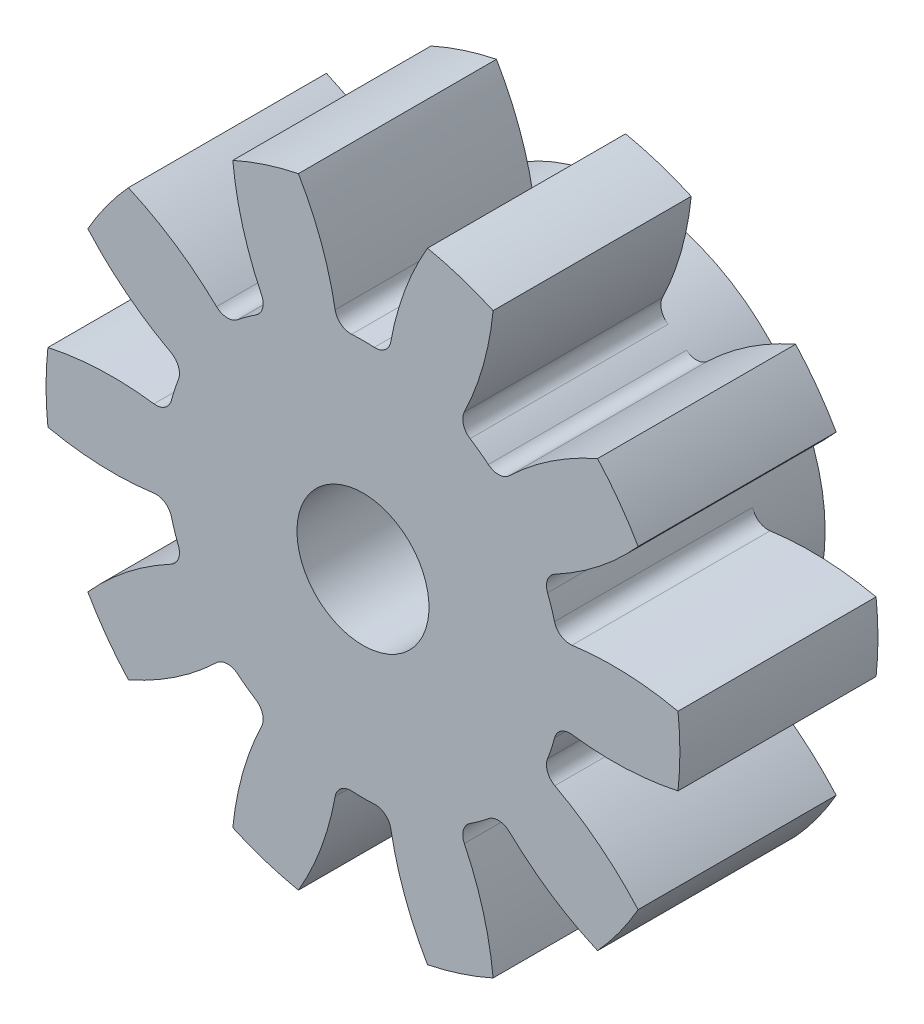
SolidWorks part; units mm, degrees
ref_plane "Front Plane" through (0, 0, 0) normal (0, 0, 1) x (1, 0, 0)
ref_plane "Top Plane" through (0, 0, 0) normal (0, 1, 0) x (1, 0, 0)
ref_plane "Right Plane" through (0, 0, 0) normal (1, 0, 0) x (0, 0, -1)
sketch "Sketch1" plane through (0, 0, 0) normal (0, 0, 1) x (1, 0, 0)
  circle A0 centre (0, 0) radius 10
  circle A1 centre (0, 0) radius 12
  circle A2 centre (0, 0) radius 7.5
  dimension "D1" = 20
  dimension "D2" = 24
  dimension "D3" = 4.5
extrude "Boss-Extrude1" add sketch "Sketch1" along normal mid plane 425 contours A1
sketch "Sketch2" plane through (0, 0, 0) normal (0, 0, 1) x (1, 0, 0)
  line L0 (0, 0) -> (0, 12) construction
  line L1 (-1.5643, 9.8769) -> (1.5643, 9.8769) construction
  line L2 (-0.9691, 7.4371) -> (0, 0) construction
  line L3 (0, 5.5789) -> (-2.6051, 12.7363) construction
  line L4 (0, 0) -> (3.7082, 11.4127) construction
  line L5 (1.5643, 9.8769) -> (4.5399, 8.9101) construction
  circle A0 centre (0, 0) radius 12 construction
  arc A1 (-3.0254, 12.6431) -> (-0.9691, 7.4371) centre (-12.3373, 5.9558) cw
  arc A2 (3.0254, 12.6431) -> (0.9691, 7.4371) centre (12.3373, 5.9558) ccw
  circle A3 centre (0, 0) radius 7.5 construction
  arc A4 (0.9691, 7.4371) -> (-0.9691, 7.4371) centre (0, 0) ccw
  circle A5 centre (0, 0) radius 12 construction
  circle A6 centre (0, 0) radius 10 construction
  circle A7 centre (0, 0) radius 13
  arc A8 (3.0254, 12.6431) -> (-3.0254, 12.6431) centre (0, 0) ccw
  dimension "D2" = 1.9081
  dimension "D3" = 20
  dimension "D4" = 18
  dimension "D1" = 1
extrude "Cut-Extrude1" cut sketch "Sketch2" against normal through all both and the other way through all
fillet "Fillet1" radius 0.6 1 edges at (-0.9691, 7.4371, 0)
fillet "Fillet2" radius 0.6 1 edges at (0.9691, 7.4371, 0)
sketch "Sketch3" plane through (0, 0, -212.5) normal (0, 0, -1) x (-1, 0, 0)
pattern_circular "CirPattern2" count 10 over 360 about axis through (0, 0, 0) along (0, 0, 1) of "Cut-Extrude1", "Fillet1", "Fillet2"
sketch "Sketch4" plane through (0, 0, -212.5) normal (0, 0, -1) x (-1, 0, 0)
  circle A0 centre (0, 0) radius 7.5
  circle A1 centre (0, 0) radius 2.5
  dimension "D1" = 5
extrude "Boss-Extrude2" add sketch "Sketch4" along normal mid plane 5 contours A0 | A1
sketch "Sketch5" plane through (0, 0, -212.5) normal (0, 0, -1) x (-1, 0, 0)
  circle A0 centre (0, 0) radius 3
extrude "Cut-Extrude2" cut sketch "Sketch5" against normal blind 32 and the other way through all
sketch "Sketch6" plane through (0, 0, 212.5) normal (0, 0, 1) x (1, 0, 0)
  circle A0 centre (0, 0) radius 7.5
  dimension "D1" = 15
extrude "Boss-Extrude3" add sketch "Sketch6" along normal mid plane 12
ref_plane "Plane1" through (0, 0, -205) normal (0, 0, -1) x (-1, 0, 0)
sketch "Sketch7" plane through (0, 0, 218.5) normal (0, 0, 1) x (1, 0, 0)
  circle A0 centre (0, 0) radius 12
extrude "Cut-Extrude3" cut sketch "Sketch7" against normal up to surface (423.5 mm away) contours A0
sketch "Sketch8" plane through (0, 0, -215) normal (0, 0, -1) x (-1, 0, 0)
  circle A0 centre (0, 0) radius 1.65
  circle A1 centre (0, 0) radius 7.5
  dimension "D1" = 3.3
extrude "Boss-Extrude4" add sketch "Sketch8" against normal up to surface (10 mm away) up to face at (-3, 0, -205)
sketch "Sketch9" plane through (0, 0, -224.2059) normal (0, 0, -1) x (-1, 0, 0)
  circle A0 centre (0, 0) radius 2.5
  dimension "D1" = 5
extrude "Cut-Extrude4" cut sketch "Sketch9" against normal through all contours A0
equation "\"Module\"= 2mm"
equation "\"Number of Teeth\"= 10"
equation "\"D1@Sketch1\"=\"Module\" * \"Number of Teeth\""
equation "\"D2@Sketch1\"=(\"Number of Teeth\" + 2) * \"Module\""
equation "\"D3@Sketch1\"=\"Module\" * if( \"Module\" = > 1.25, 2.25, 2.4)"
equation "\"D4@Sketch2\"=180 / \"Number of Teeth\""
equation "\"D1@Fillet1\"=0.3 * \"Module\""
